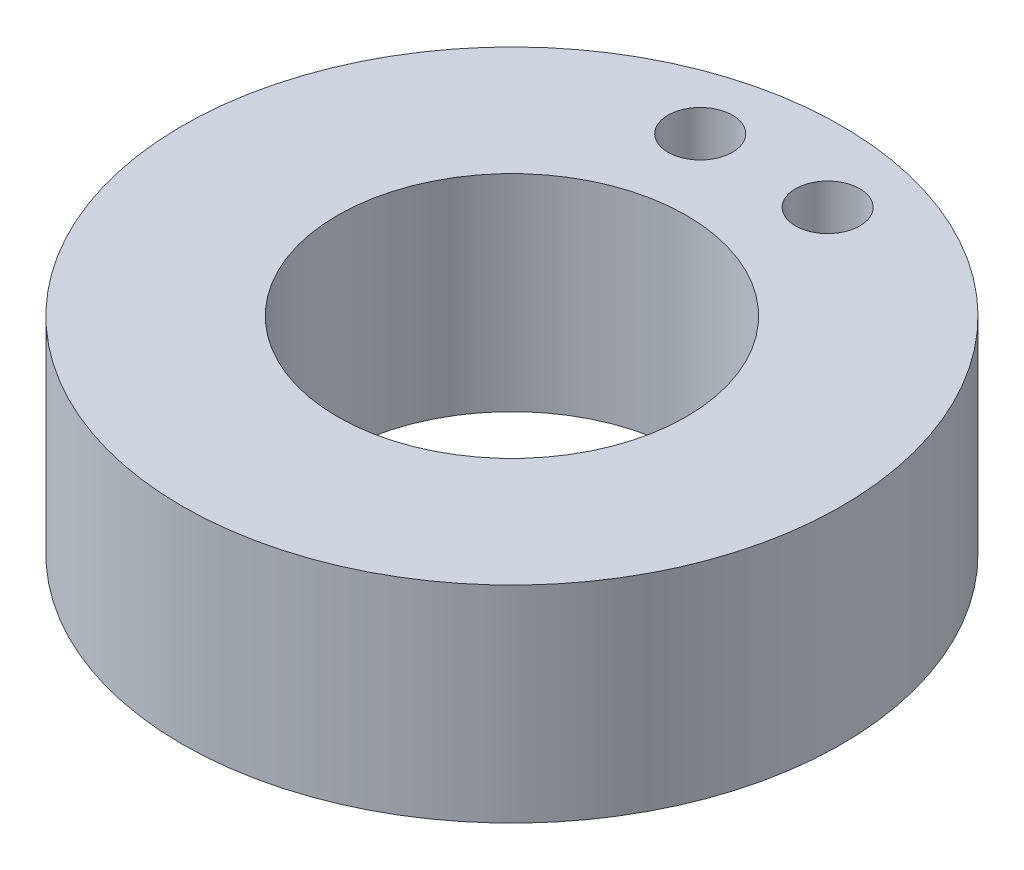
SolidWorks part; units mm, degrees
ref_plane "Front Plane" through (0, 0, 0) normal (0, 0, 1) x (1, 0, 0)
ref_plane "Top Plane" through (0, 0, 0) normal (0, 1, 0) x (1, 0, 0)
ref_plane "Right Plane" through (0, 0, 0) normal (1, 0, 0) x (0, 0, -1)
sketch "Sketch1" plane through (0, 0, 0) normal (0, 1, 0) x (1, 0, 0)
  line L0 (0, 8.5979) -> (0, 16.2433)
  circle A0 centre (0, 0) radius 8.5979
  circle A1 centre (0, 0) radius 16.2433
  dimension "D1" = 32.4866
extrude "Boss-Extrude1" add sketch "Sketch1" along normal blind 10.16
sketch "Sketch2" plane through (0, 10.16, 0) normal (0, 1, 0) x (1, 0, 0)
  line L0 (0, 12.4206) -> (-3.1403, 12.4206)
  line L2 (0, 8.5979) -> (0, 16.2433)
  circle A0 centre (0, 0) radius 16.2433 construction
  circle A1 centre (0, 0) radius 8.5979 construction
  circle A3 centre (-3.1403, 12.4206) radius 1.5875
  circle A4 centre (3.1403, 12.4206) radius 1.5875
  point P11 (-3.1403, 13.0683)
extrude "Cut-Extrude2" cut sketch "Sketch2" against normal through all
